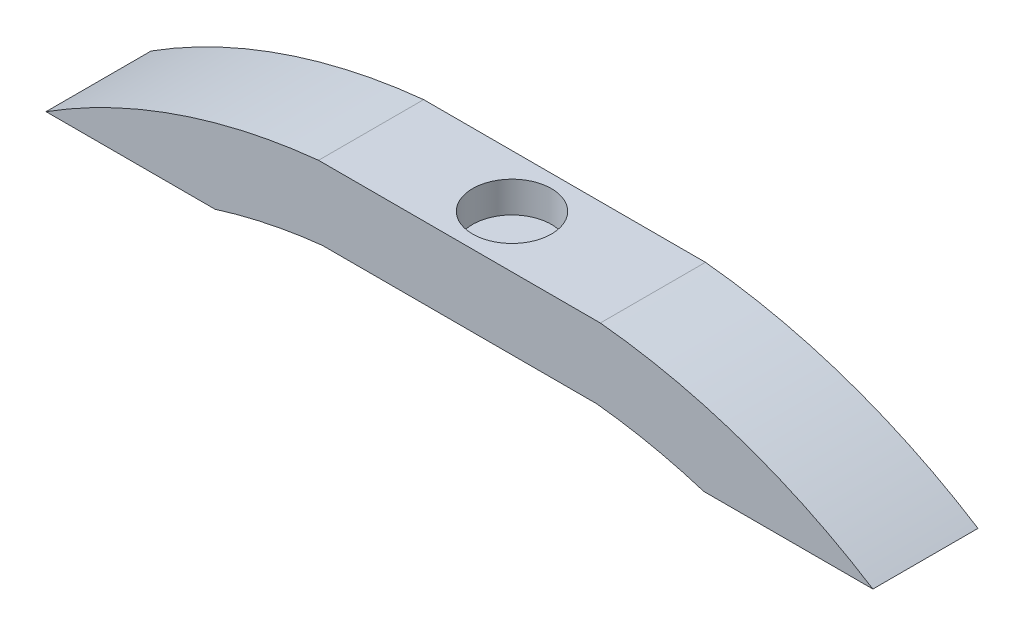
SolidWorks part; units mm, degrees
material "6061 Alloy"
ref_plane "Front Plane" through (0, 0, 0) normal (0, 0, 1) x (1, 0, 0)
ref_plane "Top Plane" through (0, 0, 0) normal (0, 1, 0) x (1, 0, 0)
ref_plane "Right Plane" through (0, 0, 0) normal (1, 0, 0) x (0, 0, -1)
sketch "Sketch1" plane through (0, 0, 0) normal (0, 0, 1) x (1, 0, 0)
  line L0 (-7.5477, 0) -> (7.5477, 0) construction
  line L1 (-13.62, 60.2648) -> (13.62, 60.2648)
  line L3 (-39.965, 51.1648) -> (39.965, 51.1648) construction
  line L4 (-13.2606, 53.3248) -> (13.2606, 53.3248)
  line L5 (-39.965, 51.1648) -> (-23.6205, 51.1648)
  line L6 (39.965, 51.1648) -> (23.6205, 51.1648)
  arc A0 (-13.62, 60.2648) -> (-39.965, 51.1648) centre (-7.5477, 0) ccw
  arc A1 (39.965, 51.1648) -> (13.62, 60.2648) centre (7.5477, 0) ccw
  arc A2 (-13.2606, 53.3248) -> (-23.6205, 51.1648) centre (-7.5477, 0) ccw
  arc A3 (23.6205, 51.1648) -> (13.2606, 53.3248) centre (7.5477, 0) ccw
  arc A4 (36.2507, 45.3025) -> (13.2606, 53.3248) centre (7.5477, 0) ccw construction
  arc A5 (-13.2606, 53.3248) -> (-36.2507, 45.3025) centre (-7.5477, 0) ccw construction
  point P3 (0, 60.2648)
  dimension "D1" = 60.57
  dimension "D2" = 79.93
  dimension "D3" = 27.24
  dimension "D4" = 9.1
  dimension "D5" = 6.94
extrude "Boss-Extrude1" add sketch "Sketch1" along normal blind 10.16
sketch "Sketch2" plane through (0, 60.2648, 0) normal (0, 1, 0) x (1, 0, 0)
  circle A0 centre (0, -5.08) radius 3.81
  dimension "D1" = 7.62
extrude "Cut-Extrude1" cut sketch "Sketch2" against normal blind 3
